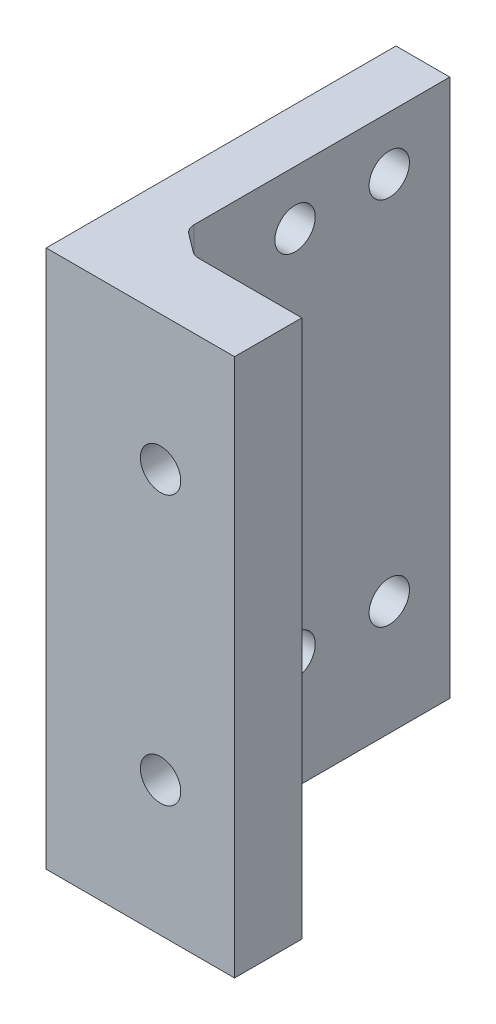
SolidWorks part; units mm, degrees
ref_plane "Front Plane" through (0, 0, 0) normal (0, 0, 1) x (1, 0, 0)
ref_plane "Top Plane" through (0, 0, 0) normal (0, 1, 0) x (1, 0, 0)
ref_plane "Right Plane" through (0, 0, 0) normal (1, 0, 0) x (0, 0, -1)
sketch "Sketch1" plane through (0, 0, 0) normal (0, 0, 1) x (1, 0, 0)
  line L6 (11, -20) -> (11, 19.3326) construction
  line L7 (15, -20) -> (11, -20)
  line L8 (15, -20) -> (15, 20)
  line L9 (15, 20) -> (11, 20)
  line L10 (11, -20) -> (11, 20)
  dimension "D1" = 11
  dimension "D2" = 4
extrude "Boss-Extrude2" add sketch "Sketch1" along normal blind 20 and the other way blind 4
sketch "Sketch3" plane through (15, 0, 0) normal (1, 0, 0) x (0, 0, -1)
  line L2 (-20, -20) -> (4, -20) construction
  line L3 (4, 20) -> (-20, 20) construction
  line L4 (-20, -20) -> (-20, 20) construction
  circle A2 centre (-0.5, -11.5) radius 1.5
  circle A3 centre (-7.5, -11.5) radius 1.5
  circle A4 centre (-0.5, 16) radius 1.5
  circle A5 centre (-7.5, 16) radius 1.5
  point P12 (0, 0)
  point P15 (0, 0)
  dimension "D1" = 3
  dimension "D3" = 3
  dimension "D4" = 4
  dimension "D5" = 19.5
  dimension "D6" = 3
  dimension "D7" = 3
  dimension "D8" = 8.5
  dimension "D2" = 7
extrude "Cut-Extrude1" cut sketch "Sketch3" against normal through all
sketch "Sketch4" plane through (15, 0, 0) normal (1, 0, 0) x (0, 0, -1)
  line L0 (-20, -20) -> (4, -20) construction
  line L1 (-20, 20) -> (-17, 20)
  line L2 (-20, 20) -> (-20, -20)
  line L3 (-20, -20) -> (-17, -20)
  line L4 (-17, 20) -> (-17, -20)
  dimension "D1" = 3
extrude "Boss-Extrude3" add sketch "Sketch4" along normal blind 10
sketch "Sketch5" plane through (0, 0, 17) normal (0, 0, -1) x (-1, 0, 0)
  line L0 (-15, -20) -> (-15, 20) construction
  line L1 (-25, -20) -> (-15, -20) construction
  line L2 (-25, 20) -> (-15, 20) construction
  circle A0 centre (-19.5, -10) radius 1.5
  circle A1 centre (-19.5, 10) radius 1.5
  point P8 (0, 0)
  point P9 (0, 0)
  dimension "D1" = 4.5
  dimension "D2" = 10
  dimension "D3" = 3
  dimension "D4" = 3
  dimension "D5" = 10
extrude "Cut-Extrude2" cut sketch "Sketch5" against normal through all
ref_plane "Plane1" through (15, 20, 17) normal (-1, 0, 0) x (0, 0, 1)
ref_plane "Plane2" through (15, 20, 17) normal (-1, 0, 0) x (0, 0, 1)
sketch "Sketch8" plane through (0, 0, 20) normal (0, 0, 1) x (1, 0, 0)
  line L1 (11, 20) -> (25, 20)
  line L2 (11, 20) -> (11, -20)
  line L3 (11, -20) -> (25, -20)
  line L4 (25, 20) -> (25, -20)
  circle A0 centre (19.5, 10) radius 1.5
  circle A1 centre (19.5, -10) radius 1.5
  dimension "D1" = 3
  dimension "D2" = 3
extrude "Boss-Extrude4" add sketch "Sketch8" along normal blind 2
sketch "Sketch9" plane through (0, -20, 0) normal (0, -1, 0) x (1, 0, 0)
  line L0 (17, 17) -> (15, 17)
  line L1 (25, 17) -> (15, 17) construction
  line L2 (15, 19.1083) -> (15, 14.8917) construction
  line L3 (15, 17) -> (15, 15.5)
  line L4 (15, 15.5) -> (17, 17)
  dimension "D1" = 2
  dimension "D2" = 1.5
extrude "Boss-Extrude5" add sketch "Sketch9" against normal up to surface (40 mm away) up to face at (17, 20, 11.6667)
fillet "Fillet3" radius 1 2 edges at (17, 0, 17) (15, 0, 15.5)
